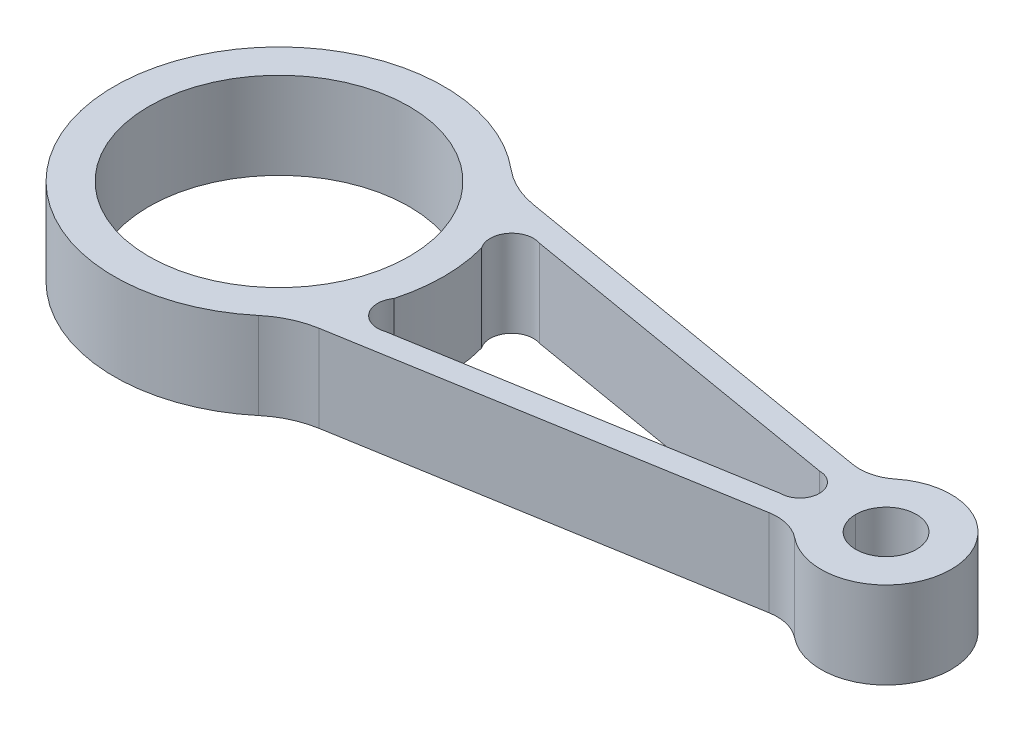
SolidWorks part; units mm, degrees
material "Plain Carbon Steel"
ref_plane "Front Plane" through (0, 0, 0) normal (0, 0, 1) x (1, 0, 0)
ref_plane "Top Plane" through (0, 0, 0) normal (0, 1, 0) x (1, 0, 0)
ref_plane "Right Plane" through (0, 0, 0) normal (1, 0, 0) x (0, 0, -1)
sketch "Sketch1" plane through (0, 0, 0) normal (0, 1, 0) x (1, 0, 0)
  line L0 (-90.7778, 30.604) -> (9.0809, 13.6541)
  line L1 (-90.7778, -20.8367) -> (9.0809, -3.8869)
  line L2 (43.5053, 4.8836) -> (-189.9895, 4.8836) construction
  circle A0 centre (-118.7504, 4.8836) radius 30
  circle A1 centre (21.2496, 4.8836) radius 15
  circle A2 centre (-118.7504, 4.8836) radius 38
  circle A3 centre (21.2496, 4.8836) radius 7
  dimension "D1" = 60
  dimension "D2" = 76
  dimension "D4" = 30
  dimension "D5" = 14
  dimension "D3" = 140
extrude "Boss-Extrude1" add sketch "Sketch1" along normal mid plane 20 contours A1 L2 A2 L1 | L2 A1 L0 A2 | L2 A1 A3 | A1 L2 A3 | L2 A2 A0 | A2 L2 A0
fillet "Fillet1" radius 10 2 edges at (9.0809, 0, 3.8869) (9.0809, 0, -13.6541)
fillet "Fillet2" radius 20 2 edges at (-90.7778, 0, -30.604) (-90.7778, 0, 20.8367)
sketch "Sketch2" plane through (0, 10, 0) normal (0, 1, 0) x (1, 0, 0)
  line L0 (-76.3857, 22.5824) -> (1.3739, 9.3836)
  line L1 (21.2496, 4.8836) -> (5.8739, 4.8836) construction
  line L2 (-76.3857, -12.8152) -> (1.3739, 0.3836)
  line L3 (-84.8092, 29.5909) -> (3.9353, 14.5275) construction
  line L4 (-84.8092, -19.8236) -> (3.9353, -4.7603) construction
  line L5 (-80.7504, 4.8836) -> (-156.7504, 4.8836) construction
  arc A0 (1.3739, 0.3836) -> (1.3739, 9.3836) centre (1.3739, 4.8836) ccw
  arc A1 (-82.1131, -5.2015) -> (-76.3857, -12.8152) centre (-78.0355, -8.0952) ccw
  arc A2 (-76.3857, 22.5824) -> (-82.1131, 14.9688) centre (-78.0355, 17.8625) ccw
  circle A3 centre (-118.7504, 4.8836) radius 30 construction
  arc A4 (-82.1131, -5.2015) -> (-82.1131, 14.9688) centre (-118.7504, 4.8836) ccw
  arc A6 (-94.3203, 33.9898) -> (-94.3203, -24.2225) centre (-118.7504, 4.8836) ccw construction
  dimension "D1" = 10
  dimension "D2" = 9
  dimension "D4" = 5.5
  dimension "D5" = 8
  dimension "D3" = 5.5
extrude "Cut-Extrude1" cut sketch "Sketch2" against normal through all
split line "Split Line1"
